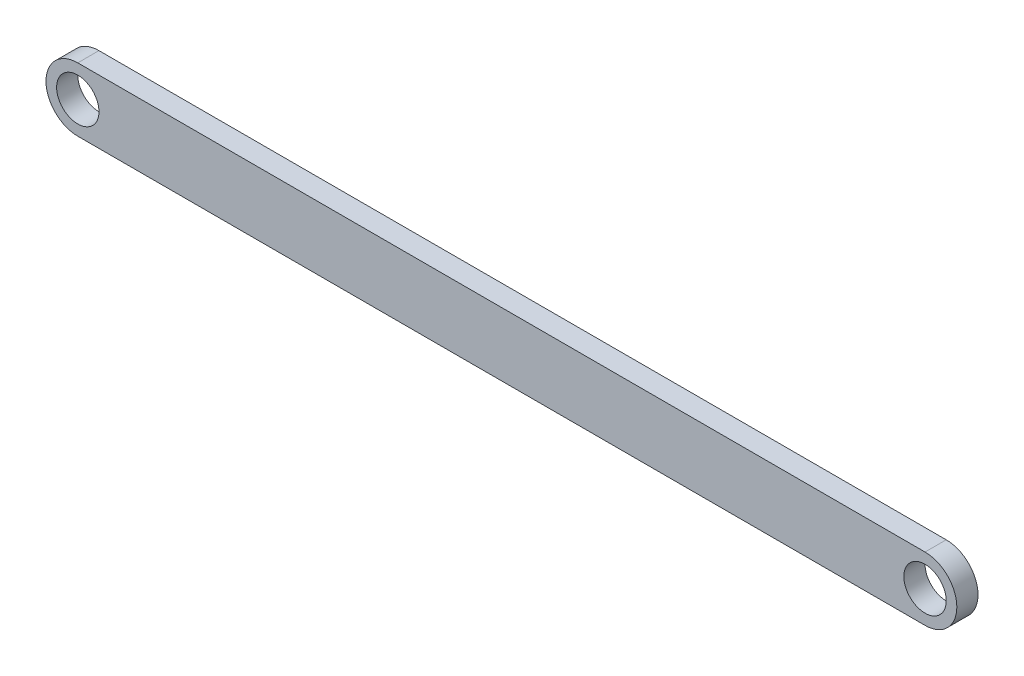
SolidWorks part; units mm, degrees
ref_plane "前视基准面" through (0, 0, 0) normal (0, 0, 1) x (1, 0, 0)
ref_plane "上视基准面" through (0, 0, 0) normal (0, 1, 0) x (1, 0, 0)
ref_plane "右视基准面" through (0, 0, 0) normal (1, 0, 0) x (0, 0, -1)
sketch "草图1" plane through (0, 0, 0) normal (0, 0, 1) x (1, 0, 0)
  line L1 (-43.6929, -3) -> (36.3071, -3)
  line L2 (-43.6929, 3) -> (36.3071, 3)
  arc A0 (36.3071, -3) -> (36.3071, 3) centre (36.3071, 0) ccw
  arc A1 (-43.6929, 3) -> (-43.6929, -3) centre (-43.6929, 0) ccw
  circle A2 centre (36.3071, 0) radius 2
  circle A3 centre (-43.6929, 0) radius 2
  dimension "D1" = 80
extrude "凸台-拉伸1" add sketch "草图1" along normal blind 2
